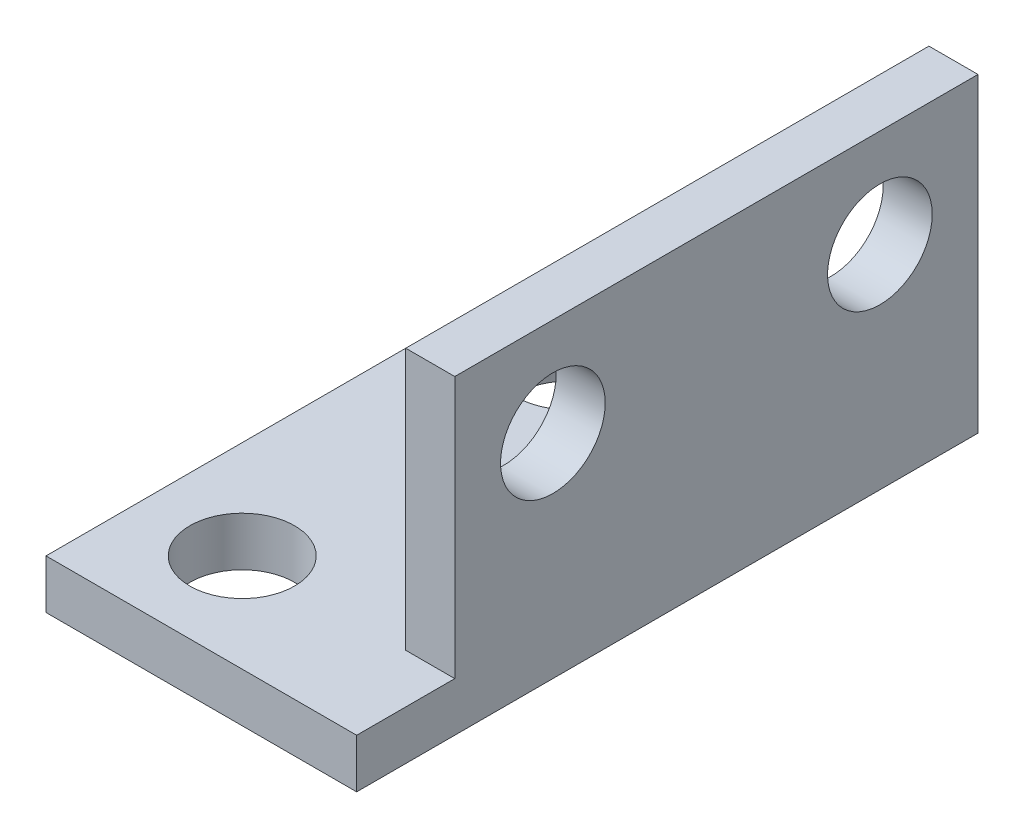
SolidWorks part; units mm, degrees
ref_plane "Front Plane" through (0, 0, 0) normal (0, 0, 1) x (1, 0, 0)
ref_plane "Top Plane" through (0, 0, 0) normal (0, 1, 0) x (1, 0, 0)
ref_plane "Right Plane" through (0, 0, 0) normal (1, 0, 0) x (0, 0, -1)
sketch "Sketch1" plane through (0, 0, 0) normal (0, 1, 0) x (1, 0, 0)
  line L4 (-3, 8) -> (-3, -13)
  line L5 (0, 8) -> (-3, 8)
  line L6 (-3, -13) -> (0, -13)
  line L8 (6.5, 0) -> (6.5, 8)
  line L9 (6.5, 8) -> (0, 8)
  line L10 (6.5, 0) -> (6.5, -13)
  line L11 (6.5, -13) -> (0, -13)
  circle A0 centre (0, 0) radius 1.6
  circle A1 centre (0, -10) radius 1.6
extrude "Boss-Extrude2" add sketch "Sketch1" along normal blind 1.5
sketch "Sketch3" plane through (0, 1.5, 0) normal (0, 1, 0) x (1, 0, 0)
  line L0 (6.5, 8) -> (5, 8)
  line L1 (6.5, 8) -> (-3, 8) construction
  line L2 (5, 8) -> (5, -13)
  line L3 (-3, -13) -> (6.5, -13) construction
  line L4 (5, -13) -> (6.5, -13)
  line L5 (6.5, -13) -> (6.5, 8)
extrude "Boss-Extrude3" add sketch "Sketch3" along normal blind 8
sketch "Sketch4" plane through (5, 0, 0) normal (-1, 0, 0) x (0, 0, 1)
  line L0 (-8, 9.5) -> (-8, 6.5)
  line L2 (-8, 9.5) -> (-8, 1.5) construction
  line L3 (-8, 6.5) -> (-5, 6.5)
  line L4 (-5, 6.5) -> (5, 6.5)
  circle A0 centre (-5, 6.5) radius 1.6
  circle A1 centre (5, 6.5) radius 1.6
extrude "Cut-Extrude2" cut sketch "Sketch4" against normal blind 8
sketch "Sketch6" plane through (5, 0, 0) normal (-1, 0, 0) x (0, 0, 1)
  line L0 (13, 9.5) -> (8, 9.5)
  line L1 (-8, 9.5) -> (13, 9.5) construction
  line L2 (8, 9.5) -> (8, 1.5)
  line L3 (-8, 1.5) -> (13, 1.5) construction
  line L4 (8, 1.5) -> (13, 1.5)
  line L5 (13, 1.5) -> (13, 9.5)
extrude "Cut-Extrude3" cut sketch "Sketch6" against normal blind 8
sketch "Sketch7" plane through (0, 1.5, 0) normal (0, 1, 0) x (1, 0, 0)
  line L0 (-3, 8) -> (-3, 3)
  line L1 (-3, 8) -> (-3, -13) construction
  line L2 (-3, 3) -> (5, 3)
  line L3 (5, 8) -> (5, -8) construction
  line L4 (5, 3) -> (5, 8)
  line L5 (5, 8) -> (-3, 8)
extrude "Cut-Extrude4" cut sketch "Sketch7" against normal blind 8
sketch "Sketch8" plane through (6.5, 0, 0) normal (1, 0, 0) x (0, 0, -1)
  line L0 (5, 6.5) -> (3, 6.5)
  line L1 (-5, 6.5) -> (-7, 6.5)
  line L2 (8, 9.5) -> (6, 9.5)
  line L3 (-8, 9.5) -> (8, 9.5) construction
  line L4 (6, 9.5) -> (6, 0)
  line L5 (-13, 0) -> (8, 0) construction
  line L6 (6, 0) -> (8, 0)
  line L7 (8, 0) -> (8, 9.5)
  circle A0 centre (-7, 6.5) radius 1.6
  circle A1 centre (3, 6.5) radius 1.6
extrude "Cut-Extrude5" cut sketch "Sketch8" against normal blind 1.5
sketch "Sketch9" plane through (6.5, 0, 0) normal (1, 0, 0) x (0, 0, -1)
  line L0 (-8, 9.5) -> (-10, 9.5)
  line L1 (-10, 9.5) -> (-10, 1.5)
  line L2 (-8, 1.5) -> (-13, 1.5) construction
  line L3 (-10, 1.5) -> (-8, 1.5)
  line L4 (-8, 1.5) -> (-8, 5.251)
  line L5 (-8, 7.749) -> (-8, 9.5)
  line L6 (6, 5.251) -> (6, 7.749)
  circle A0 centre (-7, 6.5) radius 1.6
  arc A1 (-6, 5.251) -> (-6, 7.749) centre (-5, 6.5) ccw
  arc A2 (4, 5.251) -> (6, 5.251) centre (5, 6.5) ccw
  arc A3 (4, 5.251) -> (4, 7.749) centre (3, 6.5) ccw
  arc A4 (6, 7.749) -> (4, 7.749) centre (5, 6.5) ccw
  arc M1 (6, 5.251) -> (4, 5.251) centre (5, 6.5) cw
  arc M2 (4, 5.251) -> (4, 7.749) centre (3, 6.5) cw
  arc M3 (4, 7.749) -> (6, 7.749) centre (5, 6.5) cw
  line M4 (6, 7.749) -> (6, 9.5)
  line M5 (6, 9.5) -> (-8, 9.5)
  line M6 (-8, 9.5) -> (-8, 7.749)
  arc M7 (-8, 7.749) -> (-6, 7.749) centre (-7, 6.5) cw
  arc M8 (-6, 7.749) -> (-6, 5.251) centre (-5, 6.5) cw
  arc M9 (-6, 5.251) -> (-8, 5.251) centre (-7, 6.5) cw
  line M10 (-8, 5.251) -> (-8, 1.5)
  line M11 (-8, 1.5) -> (-13, 1.5)
  line M12 (-13, 1.5) -> (-13, 0)
  line M13 (-13, 0) -> (6, 0)
  line M14 (6, 0) -> (6, 5.251)
extrude "Boss-Extrude4" add sketch "Sketch9" against normal up to surface (1.5 mm away) contours A0 L0 L1 M6 M11 M10 | A0 M8 | A3 L6 M1 M3 | M14 M1 M2 M3 M4 M5 M6 M7 M8 M9 M10 M11 M12 M13 up to face at (5, 5.2857, 0.4286)
